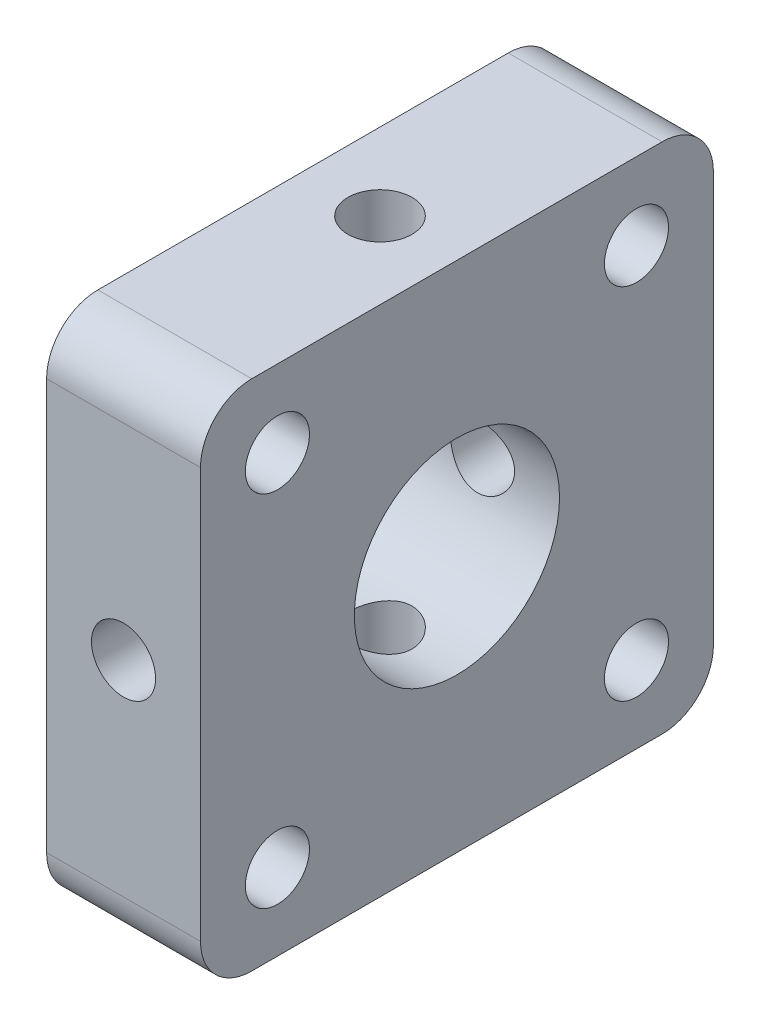
SolidWorks part; units mm, degrees
ref_plane "前视基准面" through (0, 0, 0) normal (0, 0, 1) x (1, 0, 0)
ref_plane "上视基准面" through (0, 0, 0) normal (0, 1, 0) x (1, 0, 0)
ref_plane "右视基准面" through (0, 0, 0) normal (1, 0, 0) x (0, 0, -1)
sketch "草图3" plane through (0, 0, 0) normal (1, 0, 0) x (0, 0, -1)
  line L1 (10, -10) -> (-10, -10)
  line L2 (10, -10) -> (10, 10)
  line L3 (10, 10) -> (-10, 10)
  line L4 (-10, -10) -> (-10, 10)
  line L5 (10, -10) -> (-10, 10) construction
  line L6 (10, 10) -> (-10, -10) construction
  circle A0 centre (0, 0) radius 4
  point P0 (0, 0)
  dimension "D1" = 8
  dimension "D2" = 20
  dimension "D3" = 20
extrude "凸台-拉伸2" add sketch "草图3" along normal blind 6
sketch "草图4" plane through (6, 0, 0) normal (1, 0, 0) x (0, 0, -1)
  line L0 (10, 10) -> (-10, -10) construction
  line L1 (-10, 10) -> (10, -10) construction
  line L2 (10, -10) -> (10, 10) construction
  line L3 (10, 10) -> (-10, 10) construction
  line L4 (-10, 10) -> (-10, -10) construction
  circle A0 centre (-7, 7) radius 1
  circle A1 centre (7, 7) radius 1
  circle A2 centre (-7, -7) radius 1
  circle A3 centre (7, -7) radius 1
  dimension "D1" = 2
  dimension "D2" = 2
  dimension "D3" = 2
  dimension "D4" = 2
  dimension "D5" = 3
  dimension "D6" = 3
  dimension "D7" = 3
  dimension "D8" = 3
extrude "切除-拉伸1" cut sketch "草图4" against normal up to surface (6 mm away) up to face at (0, 0, 0)
hole_wizard "M3 螺纹孔1" positions "草图5" profile "草图6" tap size "M3" standard "GB" end condition through all
sketch "草图5" plane through (0, 10, 0) normal (0, 1, 0) x (1, 0, 0)
  line L0 (6, 10) -> (6, -10) construction
  line L1 (6, -10) -> (0, -10) construction
  point P0 (3, 0)
  dimension "D1" = 3
  dimension "D2" = 10
sketch "草图6" plane through (3, 10, 0) normal (1, 0, 0) x (0, 0, 1)
  line L0 (0, 0) -> (0, 20)
  line L1 (0, 20) -> (1.25, 20)
  line L2 (1.25, 20) -> (1.25, 0)
  line L5 (1.25, 0) -> (0, 0)
  line L11 (0, -6.35) -> (0, 107.95) construction
  dimension "通孔螺纹孔钻头直径" = 2.5
  dimension "通孔螺纹孔钻头深度" = 20
cosmetic thread "孔螺蚊线1" parameters "D2"=3
hole_wizard "M3 螺纹孔2" positions "草图7" profile "草图8" tap size "M3" standard "GB" end condition through all
sketch "草图7" plane through (0, 0, -10) normal (0, 0, -1) x (-1, 0, 0)
  line L0 (0, -10) -> (0, 10) construction
  line L1 (-6, -10) -> (0, -10) construction
  point P0 (-3, 0)
  dimension "D1" = 3
  dimension "D2" = 10
sketch "草图8" plane through (3, 0, -10) normal (1, 0, 0) x (0, 1, 0)
  line L0 (0, 0) -> (0, 20)
  line L1 (0, 20) -> (1.25, 20)
  line L2 (1.25, 20) -> (1.25, 0)
  line L5 (1.25, 0) -> (0, 0)
  line L11 (0, -6.35) -> (0, 107.95) construction
  dimension "通孔螺纹孔钻头直径" = 2.5
  dimension "通孔螺纹孔钻头深度" = 20
cosmetic thread "孔螺蚊线2" parameters "D2"=3
fillet "圆角1" radius 2 4 edges at (3, -10, 10) (3, -10, -10) (3, 10, 10) (3, 10, -10)
hole_wizard "M3 螺纹孔3" positions "草图9" profile "草图10" tap size "M3" standard "GB" end condition through all
sketch "草图9" plane through (0, 0, 0) normal (-1, 0, 0) x (0, 0, 1)
  point P0 (-7, 7)
  point P3 (7, 7)
  point P6 (-7, -7)
  point P9 (7, -7)
sketch "草图10" plane through (0, 7, -7) normal (0, 1, 0) x (0, 0, 1)
  line L0 (0, 0) -> (0, 6)
  line L1 (0, 6) -> (1.25, 6)
  line L2 (1.25, 6) -> (1.25, 0)
  line L5 (1.25, 0) -> (0, 0)
  line L11 (0, -6.35) -> (0, 107.95) construction
  dimension "通孔螺纹孔钻头直径" = 2.5
  dimension "通孔螺纹孔钻头深度" = 6
cosmetic thread "孔螺蚊线3" parameters "D2"=3
cosmetic thread "孔螺蚊线4" parameters "D2"=3
cosmetic thread "孔螺蚊线5" parameters "D2"=3
cosmetic thread "孔螺蚊线6" parameters "D2"=3
